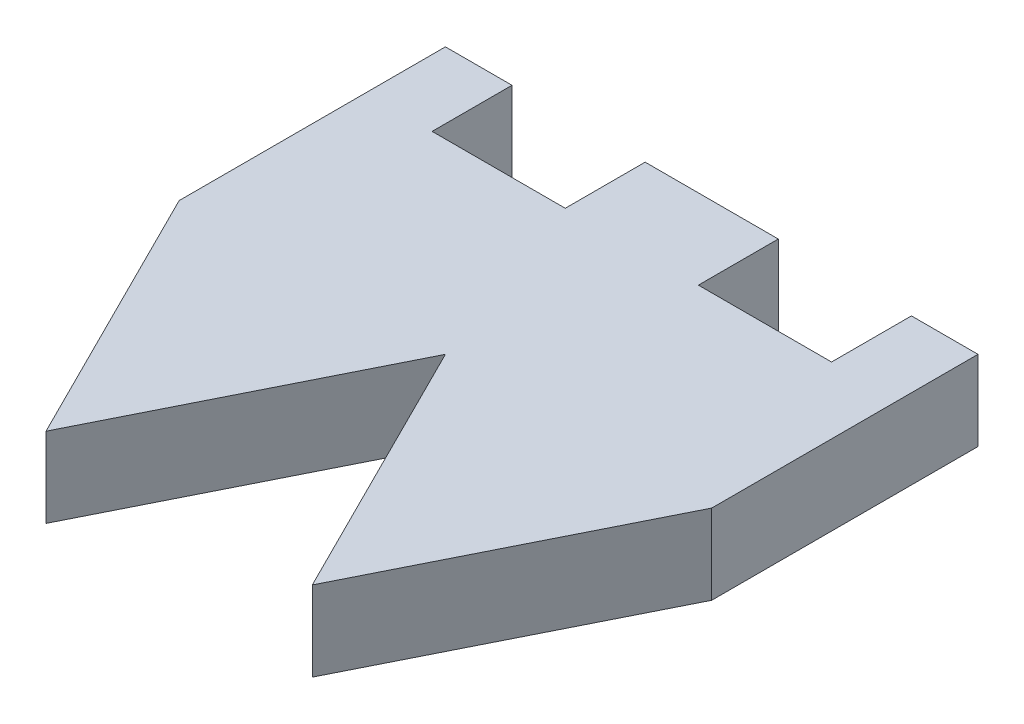
SolidWorks part; units mm, degrees
ref_plane "Front Plane" through (0, 0, 0) normal (0, 0, 1) x (1, 0, 0)
ref_plane "Top Plane" through (0, 0, 0) normal (0, 1, 0) x (1, 0, 0)
ref_plane "Right Plane" through (0, 0, 0) normal (1, 0, 0) x (0, 0, -1)
sketch "Sketch1" plane through (0, 0, 0) normal (0, 1, 0) x (1, 0, 0)
  line L1 (-10, -10) -> (10, -10)
  line L2 (-10, -10) -> (-10, 10)
  line L3 (-10, 10) -> (10, 10)
  line L4 (10, -10) -> (10, 10)
  line L5 (-10, -10) -> (10, 10) construction
  line L6 (-10, 10) -> (10, -10) construction
  point P0 (0, 0)
  dimension "D1" = 20
  dimension "D2" = 20
extrude "Boss-Extrude1" add sketch "Sketch1" along normal blind 3
sketch "Sketch2" plane through (0, 3, 0) normal (0, 1, 0) x (1, 0, 0)
  line L0 (-10, 0) -> (-5, -10)
  line L1 (-10, 10) -> (-10, -10) construction
  line L2 (-10, -10) -> (10, -10) construction
  line L3 (-5, -10) -> (0, 0)
  line L4 (0, 0) -> (5, -10)
  line L5 (5, -10) -> (10, 0)
  line L6 (10, -10) -> (10, 10) construction
  line L7 (10, 0) -> (10, -10)
  line L8 (10, -10) -> (-10, -10)
  line L9 (-10, -10) -> (-10, 0)
  line M1 (10, -10) -> (10, 10)
  line M3 (-10, 10) -> (-10, -10)
  line M4 (-10, -10) -> (10, -10)
  dimension "D1" = 5
  dimension "D2" = 5
extrude "Cut-Extrude1" cut sketch "Sketch2" against normal through all both and the other way through all contours L0 M3 M4 | L4 L3 M4 | L5 M4 M1
sketch "Sketch3" plane through (0, 3, 0) normal (0, 1, 0) x (1, 0, 0)
  line L0 (10, 10) -> (-10, 10) construction
  line L1 (-7.5, 10) -> (-2.5, 10)
  line L2 (-7.5, 10) -> (-7.5, 7)
  line L3 (-7.5, 7) -> (-2.5, 7)
  line L4 (-2.5, 10) -> (-2.5, 7)
  line L5 (-10, 10) -> (-10, 0) construction
  dimension "D1" = 3
  dimension "D2" = 5
  dimension "D3" = 2.5
extrude "Cut-Extrude2" cut sketch "Sketch3" against normal through all both and the other way through all
mirror "Mirror1" about plane through (0, 0, 0) normal (1, 0, 0) of "Cut-Extrude2"
